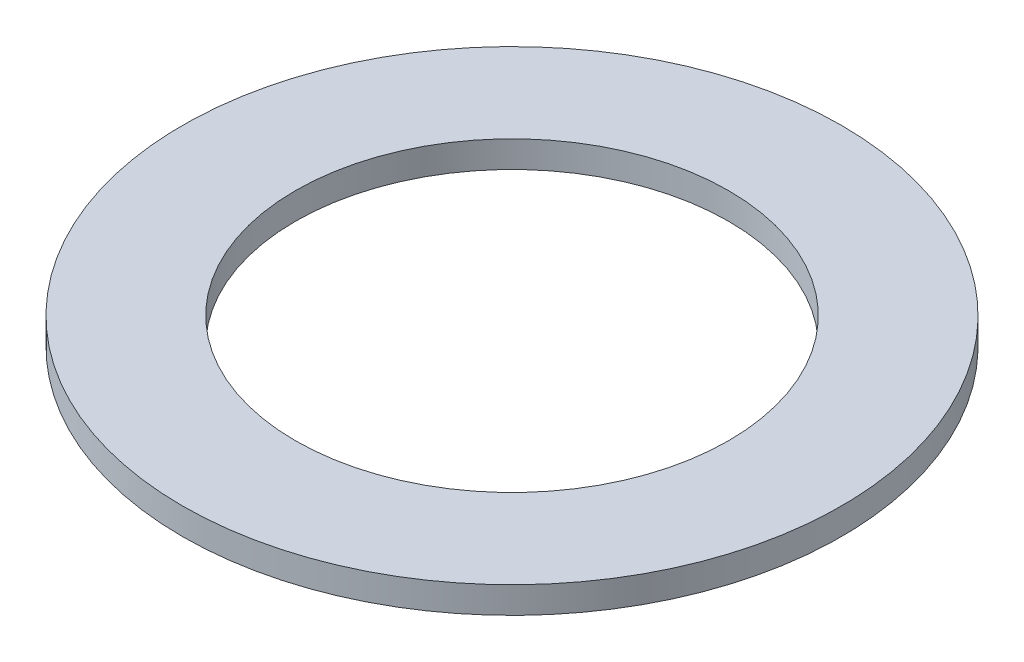
SolidWorks part; units mm, degrees
ref_plane "Front" through (0, 0, 0) normal (0, 0, 1) x (1, 0, 0)
ref_plane "Top" through (0, 0, 0) normal (0, 1, 0) x (1, 0, 0)
ref_plane "Right" through (0, 0, 0) normal (1, 0, 0) x (0, 0, -1)
sketch "Sketch1" plane through (0, 0, 0) normal (0, 1, 0) x (1, 0, 0)
  circle A0 centre (0, 0) radius 12.4
  circle A1 centre (0, 0) radius 8.15
  dimension "D1" = 16.3
  dimension "D2" = 24.8
extrude "Boss-Extrude1" add sketch "Sketch1" along normal blind 1
